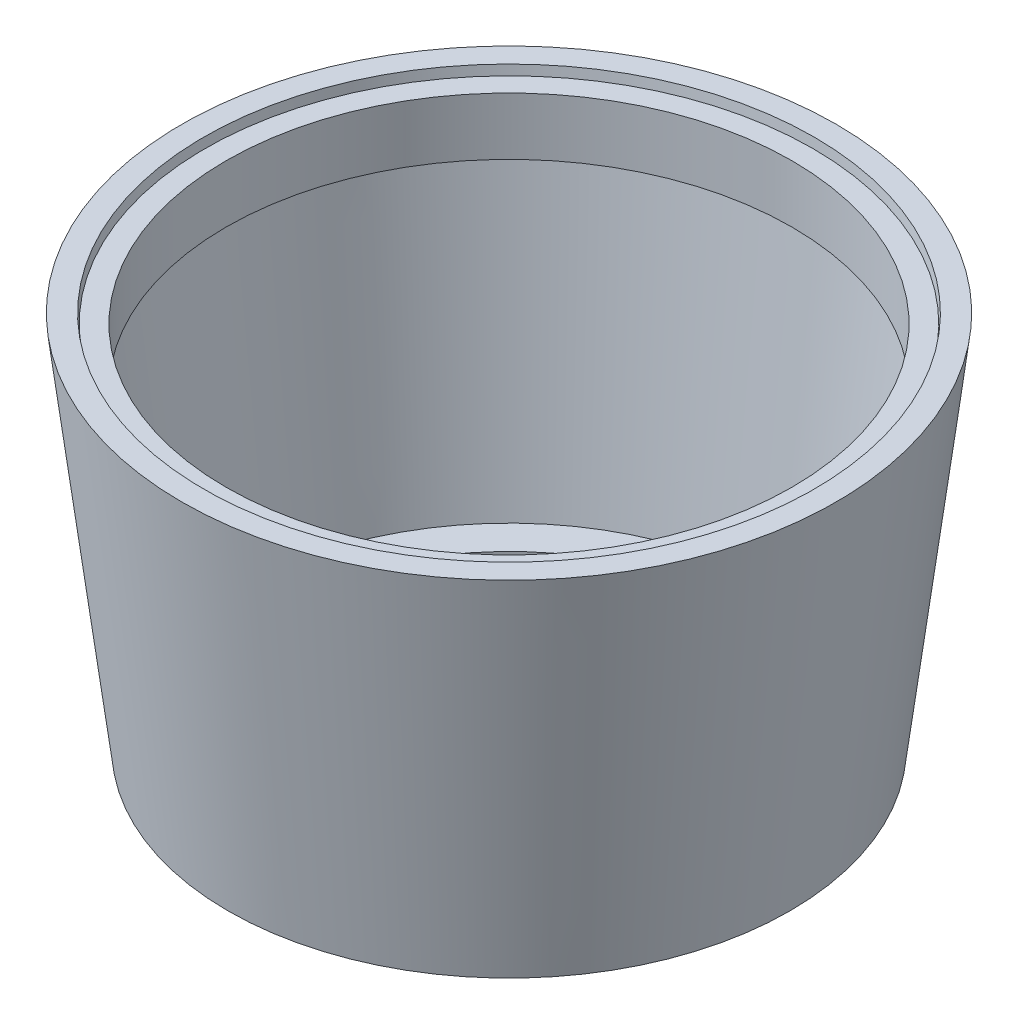
SolidWorks part; units mm, degrees
ref_plane "前视基准面" through (0, 0, 0) normal (0, 0, 1) x (1, 0, 0)
ref_plane "上视基准面" through (0, 0, 0) normal (0, 1, 0) x (1, 0, 0)
ref_plane "右视基准面" through (0, 0, 0) normal (1, 0, 0) x (0, 0, -1)
sketch "草图1" plane through (0, 0, 0) normal (0, 0, 1) x (1, 0, 0)
  line L0 (-120.2201, 0) -> (4.9344, 0)
  line L1 (-120.2201, 0) -> (-120.2201, 14)
  line L2 (4.9344, 0) -> (129.8085, 1017.0184)
  line L3 (129.8085, 1017.0184) -> (70.2195, 1017.0184)
  line L4 (70.2195, 1017.0184) -> (67.1009, 991.6196)
  line L5 (67.1009, 991.6196) -> (10.444, 991.6196)
  line L6 (10.444, 991.6196) -> (10.444, 836.7374)
  line L7 (74.3042, 836.7374) -> (-26.7152, 14)
  line L8 (10.444, 836.7374) -> (74.3042, 836.7374)
  line L9 (-120.2201, 14) -> (-26.7152, 14)
  line L10 (-120.2201, 0) -> (-752, 0) construction
  line L11 (-752, 0) -> (-752, 109.4948) construction
  point P3 (-24.4031, 658.8721)
  point P14 (0, 0)
revolve "旋转1" add sketch "草图1" angle 360 about L11
